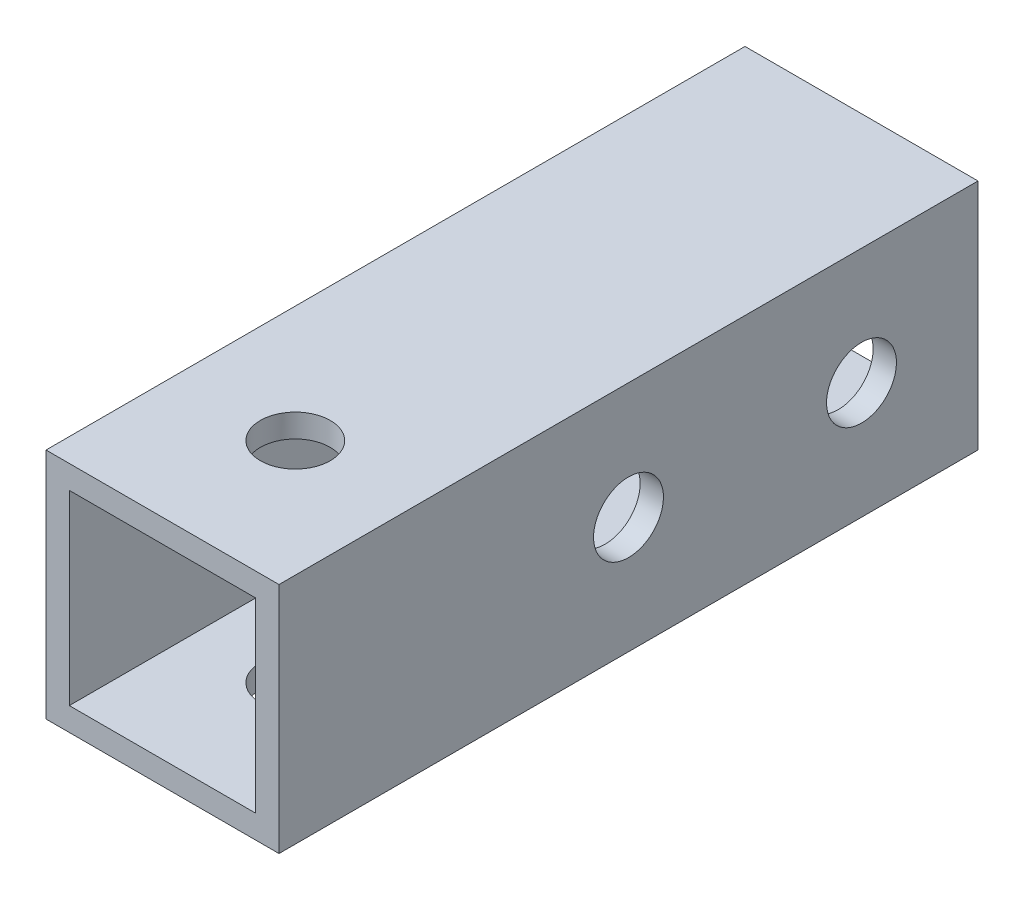
SolidWorks part; units mm, degrees
material "6063-O"
ref_plane "前视基准面" through (0, 0, 0) normal (0, 0, 1) x (1, 0, 0)
ref_plane "上视基准面" through (0, 0, 0) normal (0, 1, 0) x (1, 0, 0)
ref_plane "右视基准面" through (0, 0, 0) normal (1, 0, 0) x (0, 0, -1)
other "Configuration Table"
sketch "草图1" plane through (0, 0, 0) normal (0, 0, 1) x (1, 0, 0)
  line L1 (-5, 5) -> (5, 5)
  line L2 (-5, 5) -> (-5, -5)
  line L3 (-5, -5) -> (5, -5)
  line L4 (5, 5) -> (5, -5)
  line L5 (-5, 5) -> (5, -5) construction
  line L6 (-5, -5) -> (5, 5) construction
  point P4 (0, 0)
  dimension "D1" = 10
  dimension "D2" = 10
extrude "拉伸-薄壁1" add sketch "草图1" along normal blind 30 thin
sketch "草图2" plane through (5, 0, 0) normal (1, 0, 0) x (0, 0, -1)
  line L0 (-30, 0) -> (0, 0) construction
  line L1 (-30, -5) -> (-30, 5) construction
  circle A1 centre (-5, 0) radius 1.5
  circle A2 centre (-15, 0) radius 1.5
  dimension "D2" = 3
  dimension "D3" = 10
  dimension "D4" = 3
  dimension "D1" = 5
extrude "切除-拉伸1" cut sketch "草图2" against normal through all contours A1
sketch "草图3" plane through (0, 5, 0) normal (0, 1, 0) x (1, 0, 0)
  line L0 (0, -30) -> (0, 0) construction
  line L1 (5, -30) -> (-5, -30) construction
  line L2 (5, 0) -> (-5, 0) construction
  circle A0 centre (0, -24.3) radius 1.5
  dimension "D1" = 3
  dimension "D2" = 24.3
extrude "切除-拉伸2" cut sketch "草图3" against normal through all
